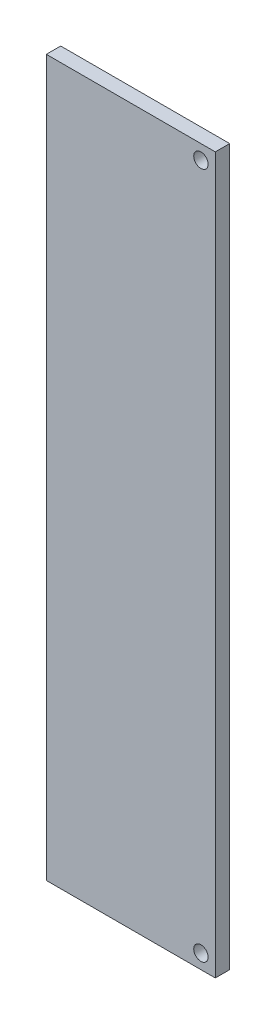
SolidWorks part; units mm, degrees
ref_plane "Front Plane" through (0, 0, 0) normal (0, 0, 1) x (1, 0, 0)
ref_plane "Top Plane" through (0, 0, 0) normal (0, 1, 0) x (1, 0, 0)
ref_plane "Right Plane" through (0, 0, 0) normal (1, 0, 0) x (0, 0, -1)
sketch "Sketch1" plane through (0, 0, 0) normal (0, 0, 1) x (1, 0, 0)
  line L1 (-57, 36) -> (-33.5, 36)
  line L2 (-57, 36) -> (-57, -63.5)
  line L3 (-57, -63.5) -> (-33.5, -63.5)
  line L4 (-33.5, 36) -> (-33.5, -63.5)
  dimension "D1" = 99.5
  dimension "D2" = 23.5
extrude "Boss-Extrude1" add sketch "Sketch1" along normal blind 2
sketch "Sketch2" plane through (0, 0, 2) normal (0, 0, 1) x (1, 0, 0)
  line L0 (-33.5, 36) -> (-57, 36) construction
  line L1 (-33.5, -63.5) -> (-33.5, 36) construction
  line L2 (-57, -63.5) -> (-33.5, -63.5) construction
  circle A0 centre (-35.5, 34) radius 1
  circle A1 centre (-35.5, -61.5) radius 1
  dimension "D1" = 2
  dimension "D2" = 2
  dimension "D3" = 2
  dimension "D4" = 2
  dimension "D5" = 2
  dimension "D6" = 2
extrude "Cut-Extrude1" cut sketch "Sketch2" against normal through all
